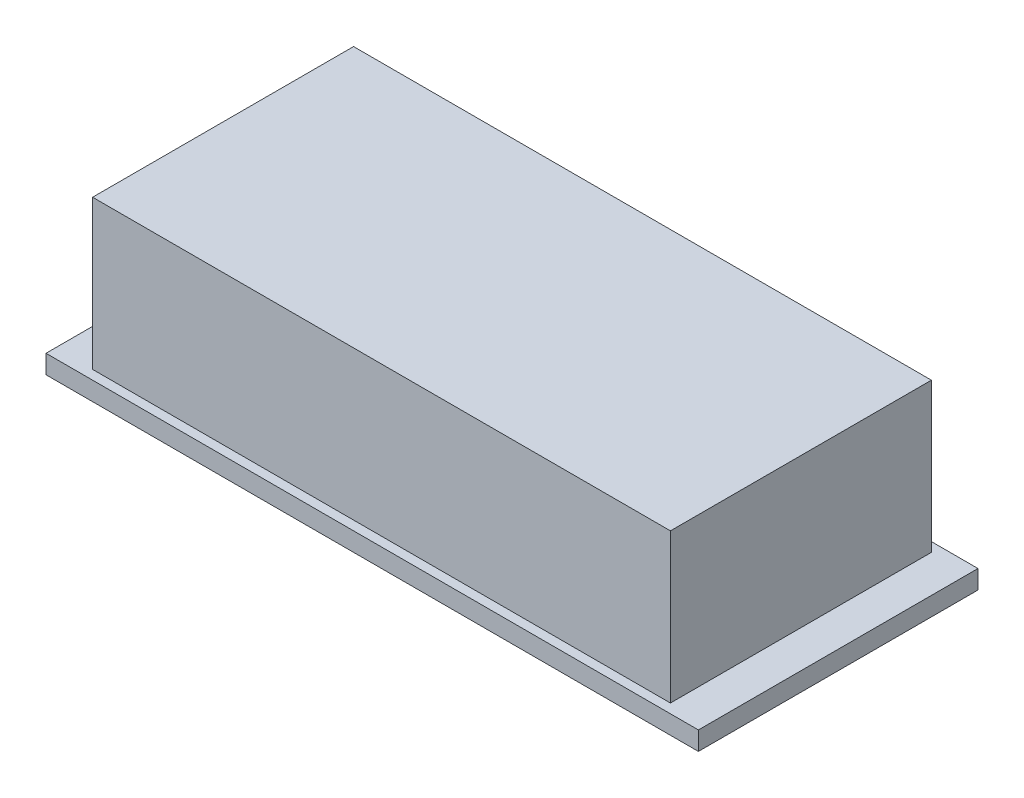
SolidWorks part; units mm, degrees
ref_plane "Plan de face" through (0, 0, 0) normal (0, 0, 1) x (1, 0, 0)
ref_plane "Plan de dessus" through (0, 0, 0) normal (0, 1, 0) x (1, 0, 0)
ref_plane "Plan de droite" through (0, 0, 0) normal (1, 0, 0) x (0, 0, -1)
sketch "Esquisse1" plane through (0, 0, 0) normal (0, 1, 0) x (1, 0, 0)
  line L1 (0, 0) -> (70, 0)
  line L2 (0, 0) -> (0, 30)
  line L3 (0, 30) -> (70, 30)
  line L4 (70, 0) -> (70, 30)
  dimension "D1" = 30
  dimension "D2" = 70
extrude "Boss.-Extru.1" add sketch "Esquisse1" along normal blind 2
sketch "Esquisse2" plane through (0, 2, 0) normal (0, 1, 0) x (1, 0, 0)
  line L0 (0, 0) -> (70, 0) construction
  line L1 (4, 29) -> (66, 29)
  line L2 (4, 29) -> (4, 1)
  line L3 (4, 1) -> (66, 1)
  line L4 (66, 29) -> (66, 1)
  line L5 (70, 30) -> (0, 30) construction
  line L6 (70, 0) -> (70, 30) construction
  line L7 (0, 30) -> (0, 0) construction
  dimension "D1" = 1
  dimension "D2" = 1
  dimension "D3" = 4
  dimension "D4" = 4
extrude "Boss.-Extru.2" add sketch "Esquisse2" along normal blind 16
